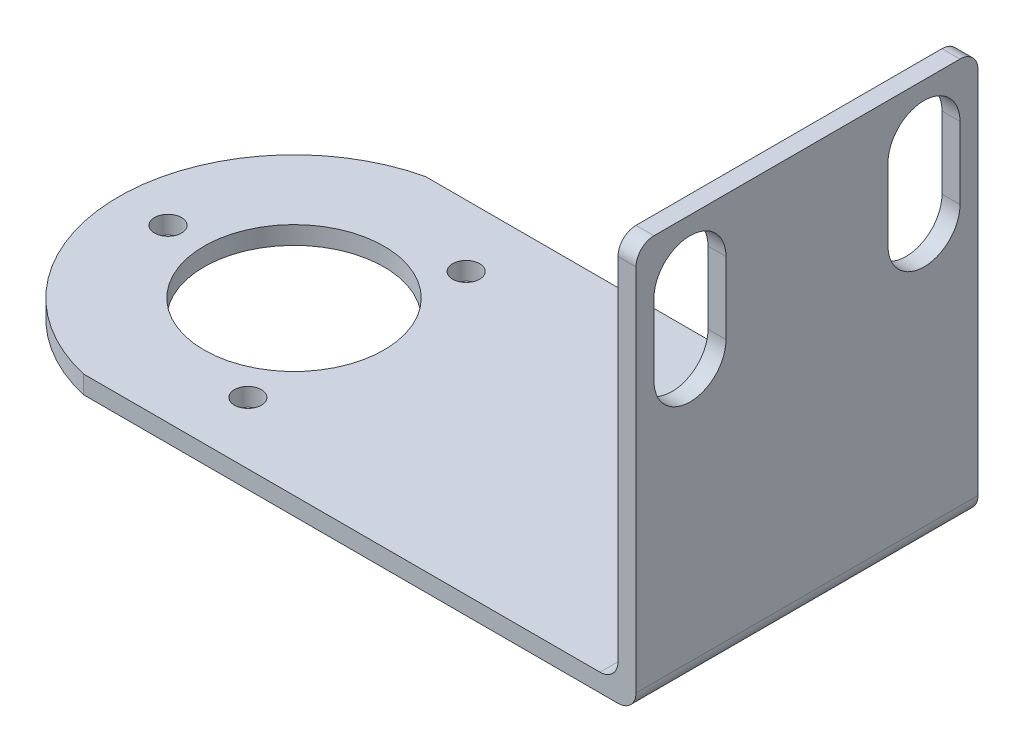
SolidWorks part; units mm, degrees
ref_plane "Front Plane" through (0, 0, 0) normal (0, 0, 1) x (1, 0, 0)
ref_plane "Top Plane" through (0, 0, 0) normal (0, 1, 0) x (1, 0, 0)
ref_plane "Right Plane" through (0, 0, 0) normal (1, 0, 0) x (0, 0, -1)
sketch "Sketch1" plane through (0, 0, 0) normal (0, 1, 0) x (1, 0, 0)
  line L1 (0, 0) -> (61.3875, 0)
  line L3 (0, 38) -> (61.3875, 38)
  line L4 (61.3875, 0) -> (61.3875, 38)
  arc A0 (0, 38) -> (0, 0) centre (4.3875, 19) ccw
  circle A1 centre (-9.6125, 19) radius 1.5
  circle A2 centre (11.3875, 31.1244) radius 1.5
  circle A3 centre (11.3875, 6.8756) radius 1.5
  circle A4 centre (4.3875, 19) radius 10
  point P9 (4.3875, 19)
  point P15 (4.3875, 19)
  dimension "D1" = 19.5
  dimension "D3" = 3
  dimension "D6" = 20
  dimension "D2" = 38
  dimension "D4" = 14
  dimension "D7" = 57
  dimension "D5" = 3
extrude "Boss-Extrude1" add sketch "Sketch1" along normal blind 2 contours L3 A0 L1 L4 A4 A2 A1
sketch "Sketch2" plane through (0, 2, 0) normal (0, 1, 0) x (1, 0, 0)
  line L0 (0, 38) -> (61.3875, 38) construction
  line L1 (61.3875, 0) -> (59.3875, 0)
  line L2 (61.3875, 0) -> (61.3875, 38)
  line L3 (61.3875, 38) -> (59.3875, 38)
  line L4 (59.3875, 0) -> (59.3875, 38)
  dimension "D1" = 2
extrude "Boss-Extrude2" add sketch "Sketch2" along normal blind 43
fillet "Fillet1" radius 2 4 edges at (60.3875, 45, 0) (60.3875, 45, -38) (59.3875, 2, -19) (61.3875, 0, -19)
sketch "Sketch3" plane through (61.3875, 0, 0) normal (1, 0, 0) x (0, 0, -1)
  line L0 (6, 39) -> (6, 31) construction
  line L1 (10, 39) -> (10, 31)
  line L2 (2, 39) -> (2, 31)
  line L3 (32, 39) -> (32, 31) construction
  line L4 (36, 39) -> (36, 31)
  line L5 (28, 39) -> (28, 31)
  line L6 (0, 43) -> (0, 2) construction
  line L7 (38, 43) -> (38, 2) construction
  line L8 (2, 45) -> (36, 45) construction
  arc A0 (10, 39) -> (2, 39) centre (6, 39) ccw
  arc A1 (2, 31) -> (10, 31) centre (6, 31) ccw
  arc A2 (36, 39) -> (28, 39) centre (32, 39) ccw
  arc A3 (28, 31) -> (36, 31) centre (32, 31) ccw
  point P2 (6, 35)
  point P7 (32, 35)
  point P18 (6, 43)
  point P21 (32, 43)
  point P22 (6, 27)
  point P23 (32, 27)
  dimension "D1" = 2
  dimension "D2" = 2
  dimension "D3" = 8
  dimension "D4" = 8
  dimension "D5" = 2
  dimension "D6" = 2
  dimension "D7" = 16
  dimension "D8" = 16
extrude "Cut-Extrude1" cut sketch "Sketch3" against normal through all
